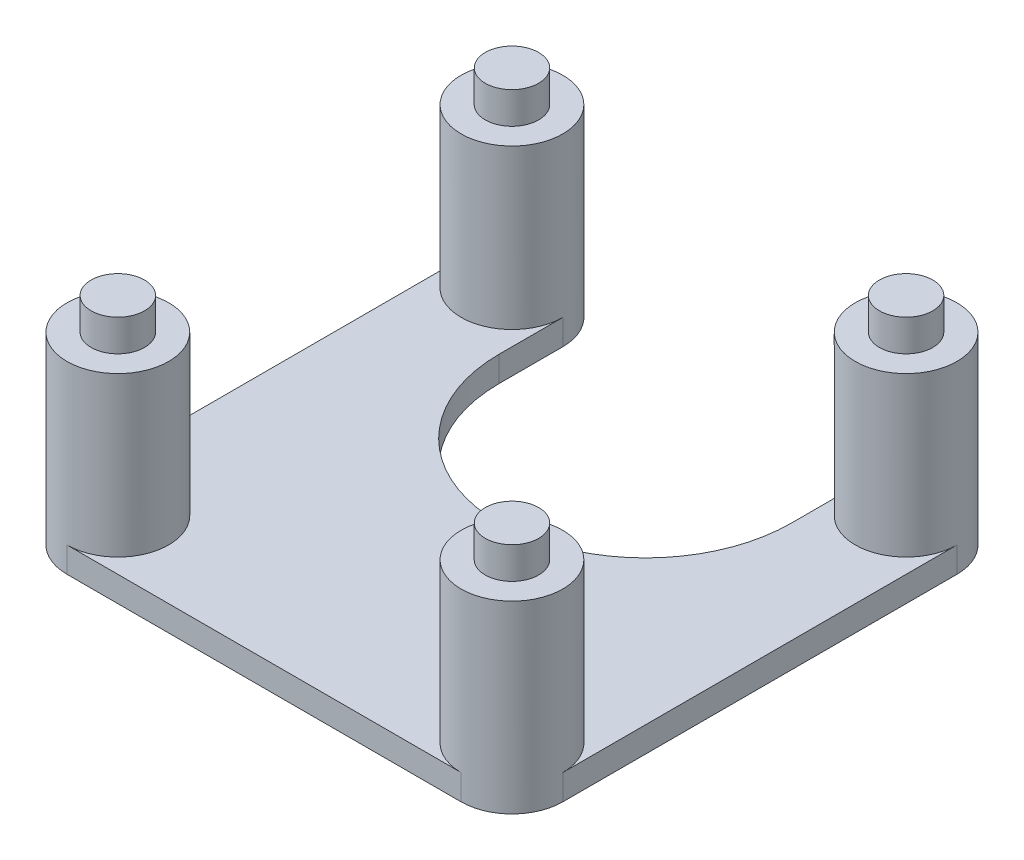
SolidWorks part; units mm, degrees
ref_plane "Front Plane" through (0, 0, 0) normal (0, 0, 1) x (1, 0, 0)
ref_plane "Top Plane" through (0, 0, 0) normal (0, 1, 0) x (1, 0, 0)
ref_plane "Right Plane" through (0, 0, 0) normal (1, 0, 0) x (0, 0, -1)
sketch "Sketch1" plane through (0, 0, 0) normal (0, 1, 0) x (1, 0, 0)
  line L0 (0, 19.4306) -> (0, 8.8753) construction
  line L5 (-9.9415, 0) -> (10.2968, 0) construction
  line L7 (-15.5, -15.5) -> (15.5, -15.5) construction
  line L8 (-15.5, -15.5) -> (-15.5, 15.5) construction
  line L9 (-15.5, 15.5) -> (15.5, 15.5) construction
  line L10 (15.5, -15.5) -> (15.5, 15.5) construction
  line L11 (-15.5, -15.5) -> (15.5, 15.5) construction
  line L12 (-15.5, 15.5) -> (15.5, -15.5) construction
  circle A0 centre (-15.5, 15.5) radius 4
  circle A1 centre (-15.5, -15.5) radius 4
  circle A2 centre (15.5, -15.5) radius 4
  circle A3 centre (15.5, 15.5) radius 4
  point P0 (0, 0)
  point P6 (0, 0)
  dimension "D5" = 8
  dimension "D3" = 31
  dimension "D4" = 31
extrude "Boss-Extrude1" add sketch "Sketch1" along normal blind 12.5 contours A1 | A0 | A2 | A3
sketch "Sketch2" plane through (0, 12.5, 0) normal (0, 1, 0) x (1, 0, 0)
  line L0 (0, 10.0509) -> (0, 6.4861) construction
  line L1 (-3.8124, 0) -> (-5.3968, 0) construction
  circle A0 centre (-15.5, 15.5) radius 2.1
  circle A1 centre (-15.5, 15.5) radius 4
  circle A2 centre (-15.5, 15.5) radius 4
  circle A3 centre (15.5, 15.5) radius 2.1
  circle A4 centre (15.5, -15.5) radius 2.1
  circle A5 centre (-15.5, -15.5) radius 2.1
  dimension "D2" = 4.2
  dimension "D1" = 0
extrude "Boss-Extrude2" add sketch "Sketch2" along normal blind 2.5 contours A0 | A3 | A4 | A5
sketch "Sketch3" plane through (0, 0, 0) normal (0, -1, 0) x (1, 0, 0)
  line L0 (-15.5, -15.5) -> (-11.5, -15.5) construction
  line L2 (-19.5, -15.5) -> (-19.5, 15.5)
  line L3 (-15.5, 19.5) -> (15.5, 19.5)
  line L4 (19.5, -15.5) -> (19.5, 15.5)
  line L5 (-11.5, -15.5) -> (-11.5, -10.4965)
  line L6 (11.5, -15.5) -> (11.5, -10.4965)
  line L7 (11.5, -15.5) -> (15.5, -15.5) construction
  circle A0 centre (-15.5, -15.5) radius 4 construction
  circle A1 centre (15.5, -15.5) radius 4 construction
  circle A2 centre (15.5, 15.5) radius 4 construction
  circle A3 centre (-15.5, 15.5) radius 4 construction
  arc A4 (-19.5, -15.5) -> (-15.5, -19.5) centre (-15.5, -15.5) ccw
  arc A5 (15.5, -19.5) -> (19.5, -15.5) centre (15.5, -15.5) ccw
  arc A6 (19.5, 15.5) -> (15.5, 19.5) centre (15.5, 15.5) ccw
  arc A7 (-15.5, 19.5) -> (-19.5, 15.5) centre (-15.5, 15.5) ccw
  arc A8 (-11.5, -10.4965) -> (11.5, -10.4965) centre (0, -10.4965) cw
  arc A9 (11.5, -15.5) -> (19.5, -15.5) centre (15.5, -15.5) ccw
  arc A10 (-19.5, -15.5) -> (-11.5, -15.5) centre (-15.5, -15.5) ccw
  point P8 (-11.5, -15.5)
  point P9 (11.5, -15.5)
  point P12 (0, 0)
  circle M12 centre (-15.5, 15.5) radius 4
  dimension "D1" = 5.0035
  dimension "D2" = 5.0035
extrude "Boss-Extrude3" add sketch "Sketch3" along normal blind 2 contours A4 A10 L5 A8 L6 A9 A5 L4 A6 L3 L2 M12 | L0 M12
